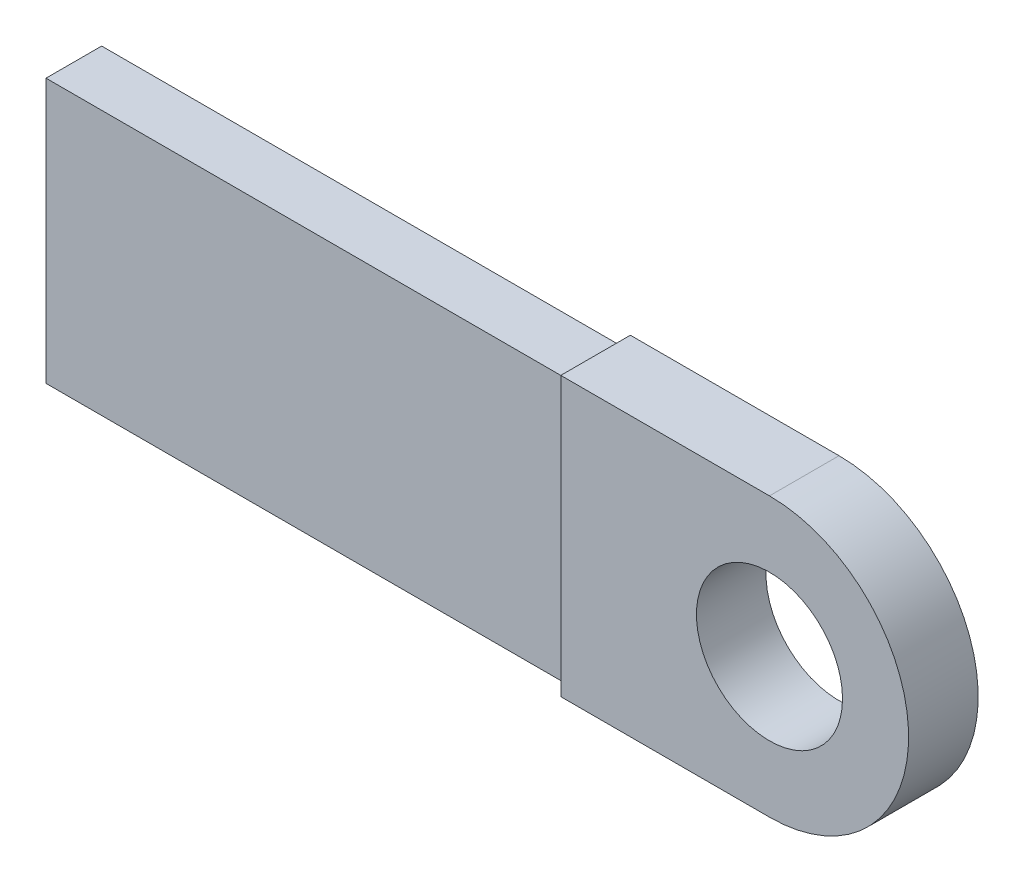
SolidWorks part; units mm, degrees
material "AISI 304"
ref_plane "Front Plane" through (0, 0, 0) normal (0, 0, 1) x (1, 0, 0)
ref_plane "Top Plane" through (0, 0, 0) normal (0, 1, 0) x (1, 0, 0)
ref_plane "Right Plane" through (0, 0, 0) normal (1, 0, 0) x (0, 0, -1)
sketch "Sketch1" plane through (0, 0, 0) normal (0, 0, 1) x (1, 0, 0)
  line L1 (0, 0) -> (100, 0)
  line L2 (0, 0) -> (0, 80)
  line L3 (0, 80) -> (100, 80)
  line L4 (100, 0) -> (100, 80)
  arc A0 (60, 80) -> (60, 0) centre (60, 40) cw
  dimension "D1" = 80
  dimension "D2" = 100
extrude "Boss-Extrude1" add sketch "Sketch1" along normal blind 20 contours A0 L3 L2 L1
sketch "Sketch2" plane through (0, 0, 20) normal (0, 0, 1) x (1, 0, 0)
  circle A0 centre (60, 40) radius 21
  arc A1 (60, 0) -> (60, 80) centre (60, 40) ccw construction
  dimension "D1" = 42
extrude "Cut-Extrude1" cut sketch "Sketch2" against normal through all
sketch "Sketch3" plane through (0, 0, 0) normal (-1, 0, 0) x (0, 0, 1)
  line L12 (2, 78) -> (2, 2)
  line L13 (2, 2) -> (18, 2)
  line L14 (18, 2) -> (18, 78)
  line L15 (18, 78) -> (2, 78)
  line L16 (2, 78) -> (2, 2)
  line L17 (2, 2) -> (18, 2)
  line L18 (18, 2) -> (18, 78)
  line L19 (18, 78) -> (2, 78)
  dimension "D1" = 2
extrude "Boss-Extrude2" add sketch "Sketch3" along normal blind 150
sketch "Sketch4" [suppressed] plane through (0, 0, 18) normal (0, 0, 1) x (1, 0, 0)
  line L0 (-150, 2) -> (-150, 78) construction
  line L1 (-150, 58) -> (-50, 58)
  line L2 (-150, 58) -> (-150, 22)
  line L3 (-150, 22) -> (-50, 22)
  line L4 (-50, 58) -> (-50, 22)
  line L5 (-150, 78) -> (0, 78) construction
  line L6 (-150, 2) -> (0, 2) construction
  dimension "D1" = 20
  dimension "D2" = 20
  dimension "D3" = 100
extrude "Cut-Extrude2" [suppressed] cut sketch "Sketch4" against normal through all
equation "\"D2@Sketch4\"=\"D1@Sketch4\""
